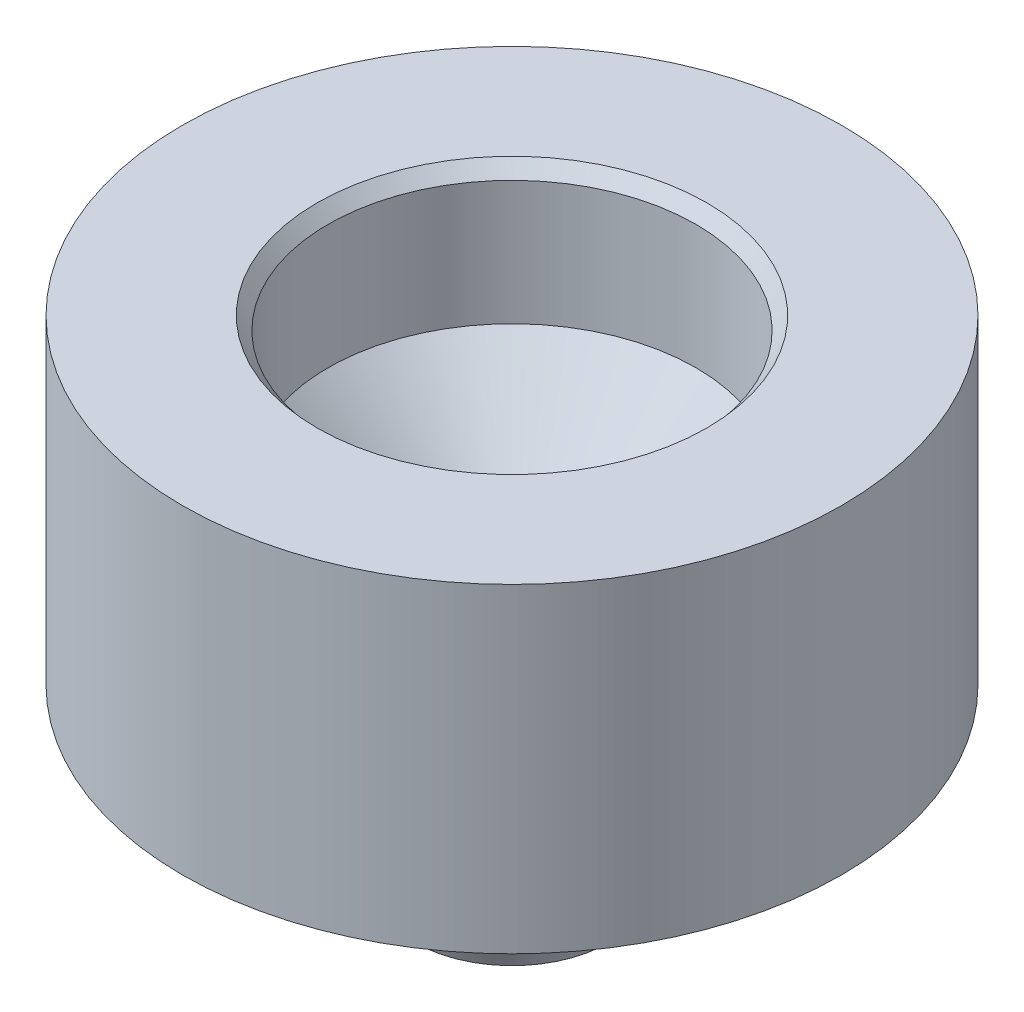
SolidWorks part; units mm, degrees
ref_plane "Front Plane" through (0, 0, 0) normal (0, 0, 1) x (1, 0, 0)
ref_plane "Top Plane" through (0, 0, 0) normal (0, 1, 0) x (1, 0, 0)
ref_plane "Right Plane" through (0, 0, 0) normal (1, 0, 0) x (0, 0, -1)
sketch "Sketch1" plane through (0, 0, 0) normal (0, 0, 1) x (1, 0, 0)
  line L0 (0, 0) -> (3.75, 0)
  line L1 (3.75, 0) -> (3.75, 6.35)
  line L2 (3.75, 6.35) -> (12, 6.35)
  line L3 (12, 6.35) -> (12, 18)
  line L4 (12, 18) -> (6.7, 18)
  line L5 (6.7, 18) -> (6.7, 10)
  line L6 (6.7, 10) -> (0, 10)
  line L7 (0, 10) -> (0, 0)
  dimension "D1" = 3.75
  dimension "D2" = 6.7
  dimension "D3" = 8
  dimension "D4" = 12
  dimension "D5" = 6.35
  dimension "D6" = 10
revolve "Revolve1" add sketch "Sketch1" angle 360 about L7
chamfer "Chamfer1" distance 3 distance2 3 1 edges at (0, 10, 6.7)
chamfer "Chamfer2" distance 0.2 angle 70 1 edges at (0, 0, 3.75)
chamfer "Chamfer3" distance 0.4 angle 50 1 edges at (0, 18, 6.7)
